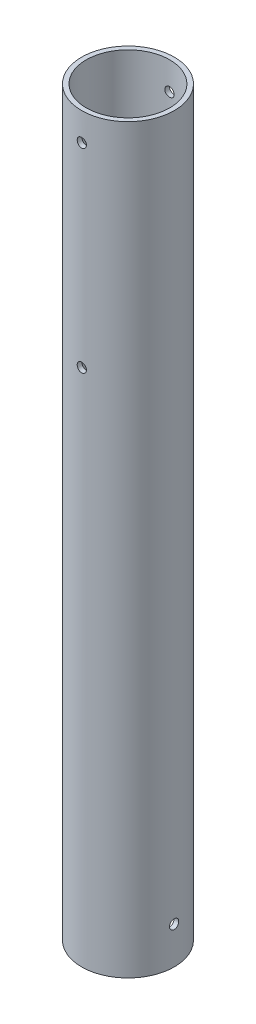
SolidWorks part; units mm, degrees
other "Markup1"
sketch "Sketch4" plane through (31.75, 0, 31.75) normal (0.2797, 0.6222, 0.7312) x (0.917, 0.0523, -0.3953)
material "6061-T6 (SS)"
ref_plane "Front Plane" through (0, 0, 0) normal (0, 0, 1) x (1, 0, 0)
ref_plane "Top Plane" through (0, 0, 0) normal (0, 1, 0) x (1, 0, 0)
ref_plane "Right Plane" through (0, 0, 0) normal (1, 0, 0) x (0, 0, -1)
sketch "Sketch1" plane through (0, 0, 0) normal (0, 1, 0) x (1, 0, 0)
  circle A0 centre (0, 0) radius 31.75
  circle A1 centre (0, 0) radius 28.575
  dimension "D1" = 3.175
  dimension "D2" = 63.5
extrude "Boss-Extrude1" add sketch "Sketch1" against normal blind 508
sketch "Sketch2" plane through (0, 0, 0) normal (0, 1, 0) x (1, 0, 0)
  line L0 (0, 0) -> (0, -31.75)
  circle A0 centre (0, 0) radius 31.75 construction
ref_plane "Plane for pins" through (0, 0, 31.75) normal (0, 0, 1) x (1, 0, 0)
sketch "Sketch3" plane through (0, 0, 31.75) normal (0, 0, 1) x (1, 0, 0)
  circle A0 centre (0, -19.05) radius 3.175
  circle A1 centre (0, -152.4) radius 3.175
  dimension "D1" = 6.35
  dimension "D4" = 6.35
  dimension "D2" = 19.05
  dimension "D3" = 152.4
extrude "Cut-Extrude1" cut sketch "Sketch3" against normal blind 508
sketch "Sketch6" plane through (0, -508, 0) normal (0, -1, 0) x (1, 0, 0)
  line L0 (28.575, 0) -> (31.75, 0)
  circle A0 centre (0, 0) radius 28.575 construction
  circle A1 centre (0, 0) radius 31.75 construction
ref_plane "Plane1" through (31.75, 0, 0) normal (1, 0, 0) x (0, 0, -1)
sketch "Sketch7" plane through (31.75, 0, 0) normal (1, 0, 0) x (0, 0, -1)
  line L0 (-31.75, -482.6) -> (31.75, -482.6) construction
  line L1 (-31.75, -508) -> (31.75, -508) construction
  line L2 (-31.75, 34.925) -> (-31.75, -34.925) construction
  line L3 (31.75, -508) -> (31.75, -155.575) construction
  circle A0 centre (0, -482.6) radius 3.175
  dimension "D2" = 6.35
  dimension "D1" = 25.4
extrude "Cut-Extrude2" cut sketch "Sketch7" against normal through all
